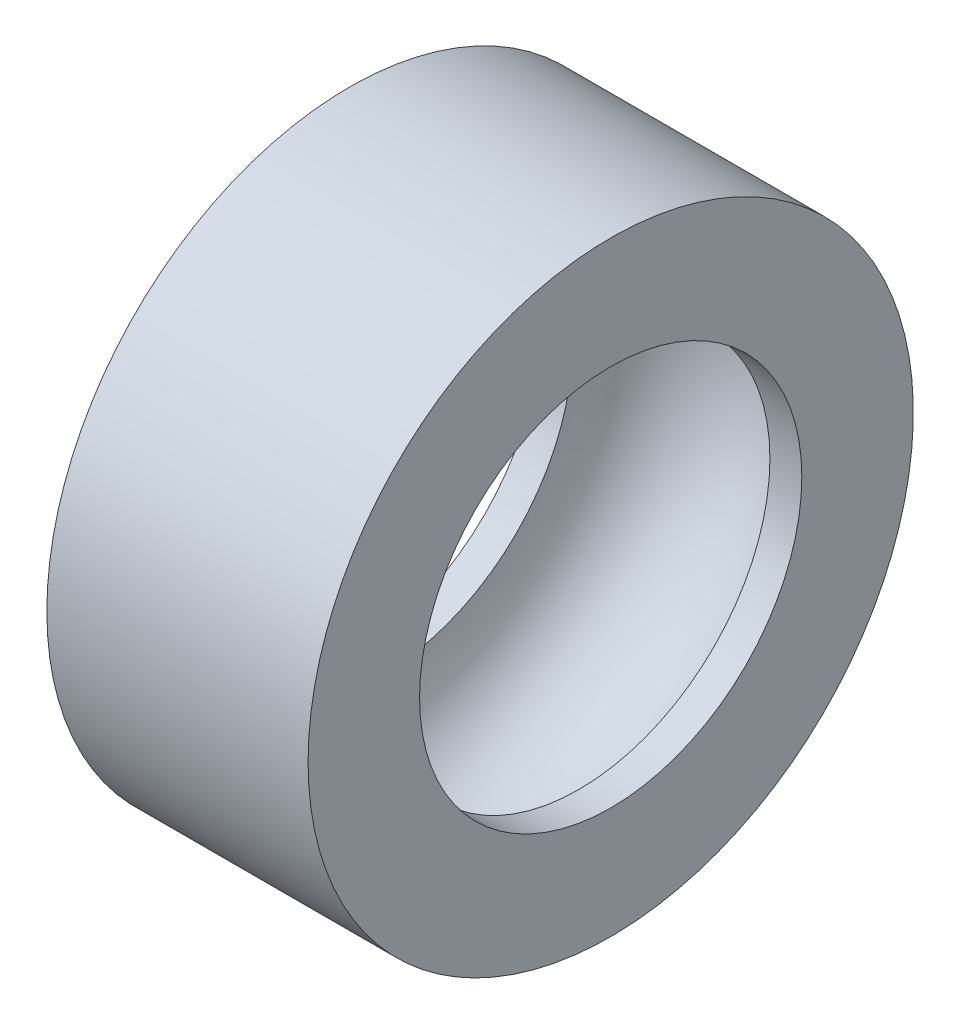
SolidWorks part; units mm, degrees
ref_plane "Front Plane" through (0, 0, 0) normal (0, 0, 1) x (1, 0, 0)
ref_plane "Top Plane" through (0, 0, 0) normal (0, 1, 0) x (1, 0, 0)
ref_plane "Right Plane" through (0, 0, 0) normal (1, 0, 0) x (0, 0, -1)
sketch "Sketch1" plane through (0, 0, 0) normal (0, 0, 1) x (1, 0, 0)
  line L0 (0, 16.6877) -> (0, 7.75) construction
  line L1 (4.1, 6) -> (3.0984, 6)
  line L2 (4.1, 6) -> (4.1, 9.5)
  line L3 (4.1, 9.5) -> (-4.1, 9.5)
  line L4 (-4.1, 6) -> (-4.1, 9.5)
  line L5 (4.1, 6) -> (-4.1, 9.5) construction
  line L6 (4.1, 9.5) -> (-4.1, 6) construction
  line L7 (-3.0984, 6) -> (-4.1, 6)
  line L8 (0, 5.5) -> (0, 0) construction
  line L9 (-10.9005, 0) -> (11.727, 0) construction
  arc A0 (3.0984, 6) -> (-3.0984, 6) centre (0, 5.9) ccw
  point P0 (0, 7.75)
  dimension "D4" = 3.1
  dimension "D1" = 6
  dimension "D2" = 3.5
  dimension "D3" = 8.2
  dimension "D5" = 0.1
revolve "Revolve1" add sketch "Sketch1" angle 360 about L9
